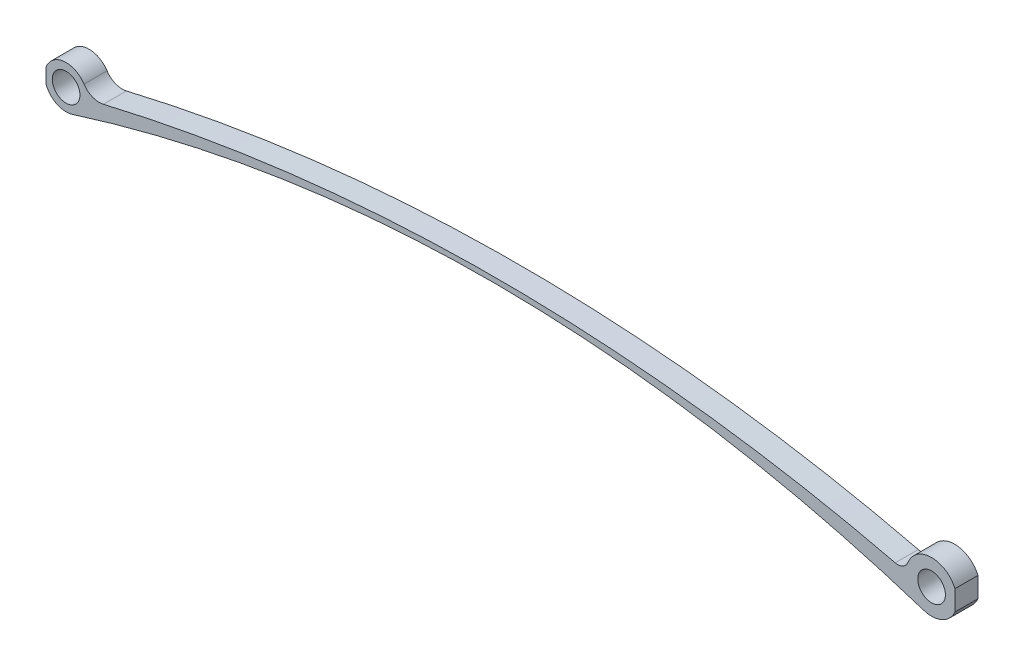
SolidWorks part; units mm, degrees
material "ABS"
ref_plane "Płaszczyzna przednia" through (0, 0, 0) normal (0, 0, 1) x (1, 0, 0)
ref_plane "Płaszczyzna górna" through (0, 0, 0) normal (0, 1, 0) x (1, 0, 0)
ref_plane "Płaszczyzna prawa" through (0, 0, 0) normal (1, 0, 0) x (0, 0, -1)
sketch "Szkic1" plane through (0, 0, 0) normal (0, 0, 1) x (1, 0, 0)
  line L0 (-3, 0) -> (187.762, 0) construction
  line L1 (92.381, 0) -> (92.381, 21.7565) construction
  circle A0 centre (0, 0) radius 3
  circle A1 centre (187.762, 0) radius 3
  arc A2 (186.046, -5.2493) -> (182.6172, 2.0075) centre (187.762, 0) ccw
  arc A3 (3.8882, 2.5232) -> (1.4006, -4.4185) centre (0, 0) ccw
  arc A4 (186.046, -5.2493) -> (1.4006, -4.4185) centre (92.4331, -291.6097) ccw
  arc A5 (179.8771, 0.5757) -> (182.6172, 2.0075) centre (180.4264, 2.8623) ccw
  arc A6 (179.8771, 0.5757) -> (8.094, 0.8374) centre (93.4373, -359.2288) ccw
  arc A7 (3.8882, 2.5232) -> (8.094, 0.8374) centre (7.187, 4.6639) ccw
  point P10 (4.6352, 0)
  point P12 (182.2394, 0)
  dimension "D1" = 187.762
  dimension "D2" = 6
  dimension "D3" = 5.5226
  dimension "D4" = 4.6352
  dimension "D5" = 6
  dimension "D6" = 2.3516
  dimension "D8" = 3.9325
extrude "Dodanie-wyciągnięcie1" add sketch "Szkic1" along normal blind 5
sketch "Szkic2" plane through (0, 0, 0) normal (0, 0, 1) x (1, 0, 0)
  line L0 (196.2931, 0) -> (-6.6873, 0) construction
  line L1 (192.8293, 4.1341) -> (192.8293, -3.3715)
  line L2 (-4.3568, -2.5646) -> (-4.3568, 2.4871)
  line L4 (-4.3568, 2.4871) -> (-5.0086, 2.4871)
  line L5 (-4.3568, 2.4871) -> (-4.3568, -2.5646)
  line L6 (-4.3568, -2.5646) -> (-5.0086, -2.5646)
  line L7 (-5.0086, 2.4871) -> (-5.0086, -2.5646)
  line L8 (192.8293, -3.3715) -> (194.4479, -3.3715)
  line L9 (192.8293, -3.3715) -> (192.8293, 4.1341)
  line L10 (192.8293, 4.1341) -> (194.4479, 4.1341)
  line L11 (194.4479, -3.3715) -> (194.4479, 4.1341)
extrude "Wytnij-wyciągnięcie3" cut sketch "Szkic2" along normal through all contours L0 L11 L10 L1 | L11 L0 L9 L8 | L0 L5 L4 L7 | L2 L0 L7 L6
